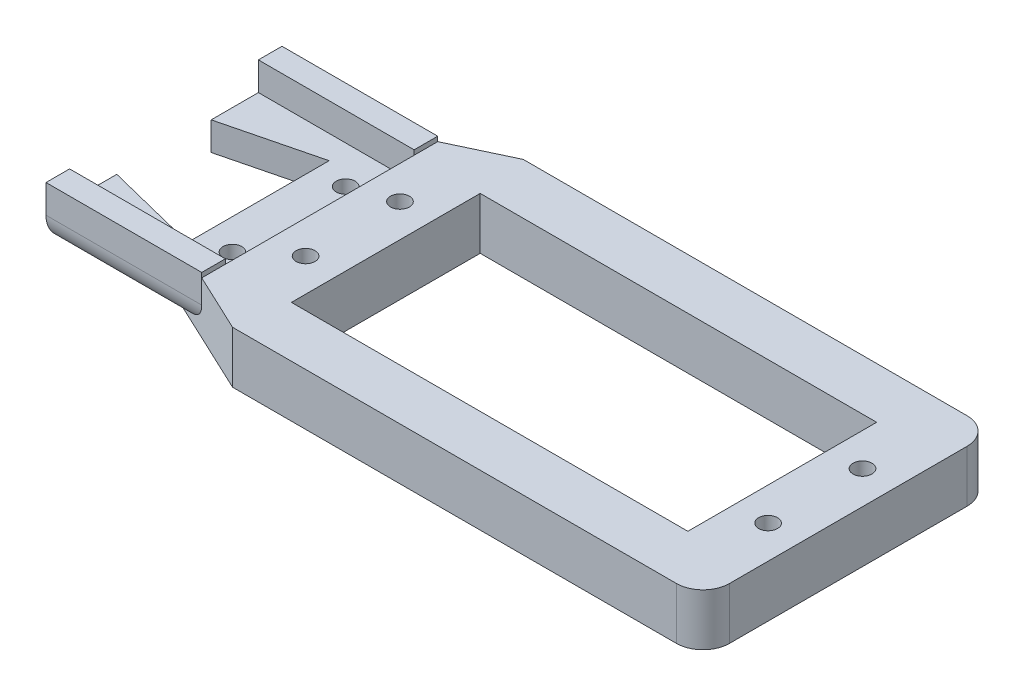
SolidWorks part; units mm, degrees
ref_plane "Alzado" through (0, 0, 0) normal (0, 0, 1) x (1, 0, 0)
ref_plane "Planta" through (0, 0, 0) normal (0, 1, 0) x (1, 0, 0)
ref_plane "Vista lateral" through (0, 0, 0) normal (1, 0, 0) x (0, 0, -1)
sketch "Croquis1" plane through (0, 0, 0) normal (0, 1, 0) x (1, 0, 0)
  line L0 (-35.5033, 12.6239) -> (-35.5033, 5.1241)
  line L1 (-35.5033, 5.1241) -> (-25.5043, 7.6239)
  line L2 (-25.5043, 7.6239) -> (-25.5043, -7.3761)
  line L3 (-25.5043, -7.3761) -> (-35.5033, -4.8764)
  line L4 (-35.5033, -4.8764) -> (-35.5033, -12.3761)
  line L5 (-35.5033, -12.3761) -> (-19.0033, -12.3761)
  line L6 (-19.0033, -12.3761) -> (-12.8396, -15.2761)
  line L7 (-12.8396, -15.2761) -> (34.184, -15.2702)
  line L8 (36.9897, -12.4645) -> (36.9897, 12.7122)
  line L9 (34.184, 15.5179) -> (-12.8396, 15.5239)
  line L10 (-12.8396, 15.5239) -> (-19.0033, 12.6239)
  line L11 (-19.0033, 12.6239) -> (-35.5033, 12.6239)
  line L12 (-12.0043, 10.1239) -> (29.9957, 10.1239)
  line L13 (-12.0043, 10.1239) -> (-12.0043, -9.8761)
  line L14 (-12.0043, -9.8761) -> (29.9957, -9.8761)
  line L15 (29.9957, 10.1239) -> (29.9957, -9.8761)
  arc A0 (34.184, -15.2702) -> (36.9897, -12.4645) centre (34.1837, -12.4642) ccw
  arc A1 (36.9897, 12.7122) -> (34.184, 15.5179) centre (34.184, 12.7122) ccw
  circle A2 centre (-22.2543, 6.1239) radius 1
  circle A3 centre (-15.5043, 5.1239) radius 1
  circle A4 centre (33.4957, 5.1239) radius 1
  circle A5 centre (33.4957, -4.8761) radius 1
  circle A6 centre (-15.5043, -4.8761) radius 1
  circle A7 centre (-22.2543, -5.8761) radius 1
extrude "Saliente-Extruir1" add sketch "Croquis1" along normal blind 5.5
sketch "Croquis2" plane through (0, 5.5, 0) normal (0, 1, 0) x (1, 0, 0)
  line L0 (-12.0043, 0.1239) -> (-37.1156, 0.1239) construction
  line L1 (-35.5033, -12.3761) -> (-19.0033, -12.3761)
  line L2 (-35.5033, -12.3761) -> (-35.5033, -9.8761)
  line L3 (-35.5033, -9.8761) -> (-19.0033, -9.8761)
  line L4 (-19.0033, -12.3761) -> (-19.0033, -9.8761)
  line L5 (-12.0043, 10.1239) -> (-12.0043, -9.8761) construction
  line L6 (-19.0033, 12.6239) -> (-19.0033, 10.1239)
  line L7 (-35.5033, 10.1239) -> (-19.0033, 10.1239)
  line L8 (-35.5033, 12.6239) -> (-35.5033, 10.1239)
  line L9 (-35.5033, 12.6239) -> (-19.0033, 12.6239)
  dimension "D1" = 2.5
extrude "Saliente-Extruir2" add sketch "Croquis2" along normal blind 0.5
sketch "Croquis3" plane through (0, 5.5, 0) normal (0, 1, 0) x (1, 0, 0)
  line L1 (-35.5033, 10.1239) -> (-19.0033, 10.1239)
  line L2 (-35.5033, 10.1239) -> (-35.5033, -9.8761)
  line L3 (-35.5033, -9.8761) -> (-19.0033, -9.8761)
  line L4 (-19.0033, 10.1239) -> (-19.0033, -9.8761)
extrude "Cortar-Extruir1" cut sketch "Croquis3" against normal blind 2.5
fillet "Redondeo1" radius 3 2 edges at (-27.2533, 0, -12.6239) (-27.2533, 0, 12.3761)
